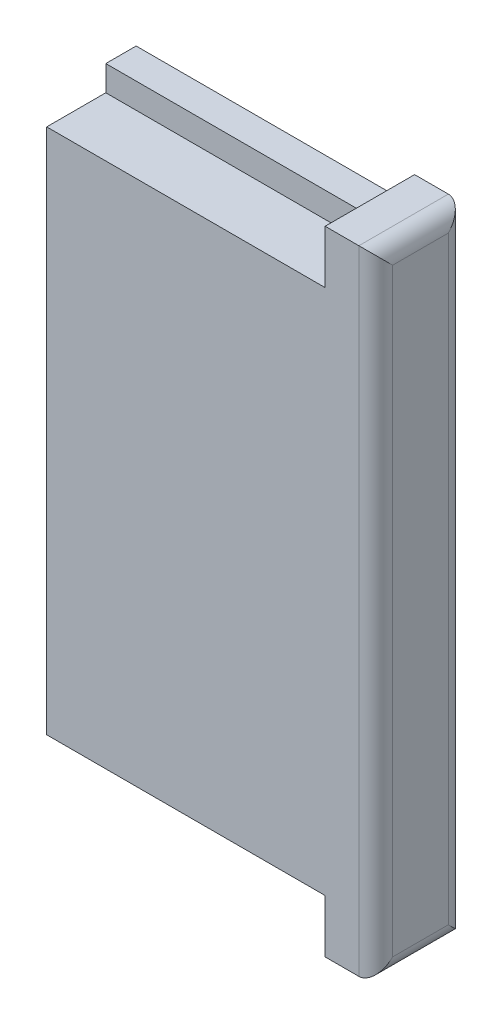
SolidWorks part; units mm, degrees
ref_plane "Piano frontale" through (0, 0, 0) normal (0, 0, 1) x (1, 0, 0)
ref_plane "Piano superiore" through (0, 0, 0) normal (0, 1, 0) x (1, 0, 0)
ref_plane "Piano destro" through (0, 0, 0) normal (1, 0, 0) x (0, 0, -1)
sketch "Sketch1" plane through (0, 0, 0) normal (0, 0, 1) x (1, 0, 0)
  line L0 (-8.25, 17.1) -> (8.25, -17.1) construction
  line L1 (-8.25, 17.1) -> (8.25, 17.1)
  line L2 (-8.25, 17.1) -> (-8.25, -17.1)
  line L3 (-8.25, -17.1) -> (8.25, -17.1)
  line L4 (8.25, 17.1) -> (8.25, -17.1)
  point P4 (0, 0)
  dimension "D1" = 34.2
  dimension "D2" = 16.5
extrude "Int" add sketch "Sketch1" along normal blind 1.8
sketch "Sketch2" plane through (0, 0, 1.8) normal (0, 0, 1) x (1, 0, 0)
  line L0 (8.25, -17.1) -> (8.25, 17.1) construction
  line L1 (8.25, 15.6) -> (-8.25, 15.6)
  line L2 (8.25, 15.6) -> (8.25, -15.6)
  line L3 (8.25, -15.6) -> (-8.25, -15.6)
  line L4 (-8.25, 15.6) -> (-8.25, -15.6)
  line L5 (8.25, 17.1) -> (-8.25, 17.1) construction
  line L6 (-8.25, -17.1) -> (8.25, -17.1) construction
  line L7 (-8.25, 17.1) -> (-8.25, -17.1) construction
  dimension "D1" = 1.5
  dimension "D2" = 1.5
extrude "Ext" add sketch "Sketch2" along normal blind 3.5
sketch "Sketch3" plane through (8.25, 0, 0) normal (1, 0, 0) x (0, 0, -1)
  line L0 (0, -17.1) -> (0, 17.1) construction
  line L1 (0, 18.75) -> (-5.3, 18.75)
  line L2 (0, 18.75) -> (0, -18.75)
  line L3 (0, -18.75) -> (-5.3, -18.75)
  line L4 (-5.3, 18.75) -> (-5.3, -18.75)
  line L5 (-5.3, -15.6) -> (-5.3, 15.6) construction
  line L6 (0, 0) -> (-5.3, 0) construction
  point P12 (-5.3, 0)
  dimension "D1" = 37.5
extrude "Top" add sketch "Sketch3" along normal blind 3
fillet "Fillet1" radius 1 4 edges at (11.25, -18.75, 2.65) (11.25, 0, 5.3) (11.25, 18.75, 2.65) (11.25, 0, 0)
